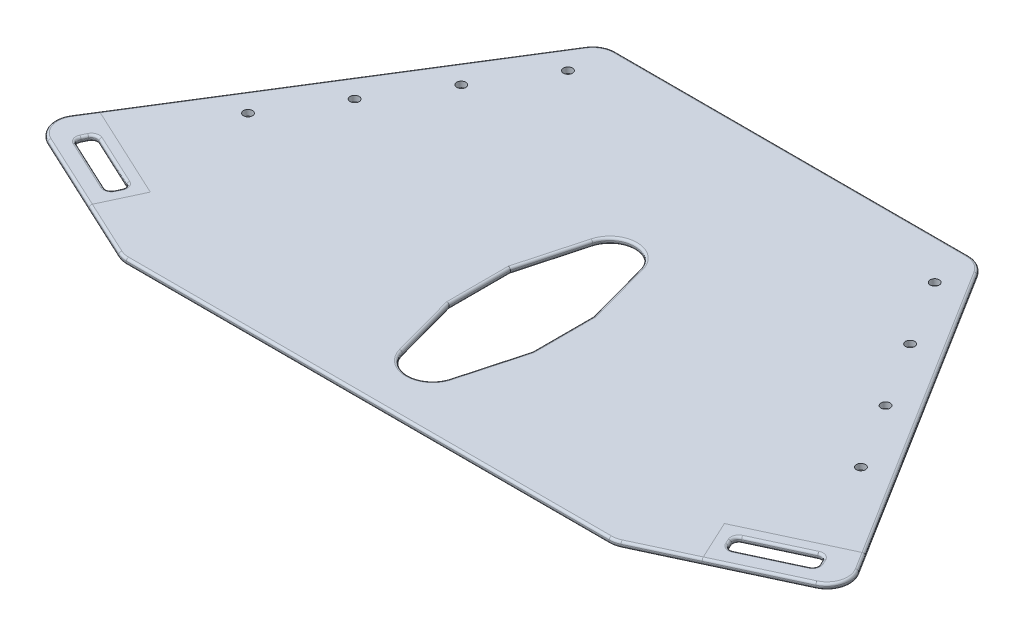
SolidWorks part; units mm, degrees
material "6061 Alloy"
ref_plane "Front Plane" through (0, 0, 0) normal (0, 0, 1) x (1, 0, 0)
ref_plane "Top Plane" through (0, 0, 0) normal (0, 1, 0) x (1, 0, 0)
ref_plane "Right Plane" through (0, 0, 0) normal (1, 0, 0) x (0, 0, -1)
sketch "Sketch1" plane through (0, 0, 0) normal (0, 1, 0) x (1, 0, 0)
  line L0 (0, -251.3064) -> (0, 218.5936) construction
  line L1 (451.3883, -168.1459) -> (273.05, -251.3064)
  line L2 (-451.3883, -168.1459) -> (-209.55, 218.5936)
  line L3 (-209.55, 218.5936) -> (0, 218.5936)
  line L4 (209.55, 218.5936) -> (0, 218.5936)
  line L5 (451.3883, -168.1459) -> (209.55, 218.5936)
  line L6 (-202.1219, 199.0782) -> (-377.1932, -80.8898) construction
  line L7 (-273.05, -251.3064) -> (-451.3883, -168.1459)
  line L8 (273.05, -251.3064) -> (-273.05, -251.3064)
  line L9 (0, -55) -> (0, 55) construction
  line L23 (46.0374, -47.3802) -> (26.459, 24.1588)
  line L24 (46.0374, -115.1266) -> (46.0374, -47.3802)
  line L25 (26.459, -186.6656) -> (46.0374, -115.1266)
  line L26 (-46.0374, -115.1266) -> (-26.459, -186.6656)
  line L27 (-46.0374, -47.3802) -> (-46.0374, -115.1266)
  line L28 (-26.459, 24.1588) -> (-46.0374, -47.3802)
  line L29 (46.0374, -47.3802) -> (26.459, 24.1588)
  line L30 (46.0374, -115.1266) -> (46.0374, -47.3802)
  line L31 (26.459, -186.6656) -> (46.0374, -115.1266)
  line L32 (-46.0374, -115.1266) -> (-26.459, -186.6656)
  line L33 (-46.0374, -47.3802) -> (-46.0374, -115.1266)
  line L34 (-26.459, 24.1588) -> (-46.0374, -47.3802)
  arc A4 (26.459, 24.1588) -> (-26.459, 24.1588) centre (0, 16.9176) ccw
  arc A5 (-26.459, -186.6656) -> (26.459, -186.6656) centre (0, -179.4244) ccw
  arc A6 (26.459, 24.1588) -> (-26.459, 24.1588) centre (0, 16.9176) ccw
  arc A7 (-26.459, -186.6656) -> (26.459, -186.6656) centre (0, -179.4244) ccw
  dimension "D2" = 419.1
  dimension "D3" = 469.9
  dimension "D4" = 44.45
  dimension "D5" = 546.1
  dimension "D6" = 65
  dimension "D1" = 6.35
extrude "Boss-Extrude1" add sketch "Sketch1" along normal blind 6.35
sketch "Sketch2" plane through (0, 6.35, 0) normal (0, 1, 0) x (1, 0, 0)
  line L0 (-342.9, -197.7155) -> (-411.9607, -165.512)
  line L1 (-342.9, -197.7155) -> (-334.8491, -180.4503)
  line L2 (-411.9607, -165.512) -> (-403.9098, -148.2468)
  line L3 (-334.8491, -180.4503) -> (-403.9098, -148.2468)
  line L4 (-342.9, -197.7155) -> (-403.9098, -148.2468) construction
  line L5 (-411.9607, -165.512) -> (-334.8491, -180.4503) construction
  line L6 (-451.3883, -168.1459) -> (-273.05, -251.3064) construction
  point P1 (-373.4049, -172.9811)
  dimension "D1" = 19.05
  dimension "D2" = 76.2
  dimension "D3" = 19.05
  dimension "D4" = 69.85
extrude "Cut-Extrude1" cut sketch "Sketch2" against normal through all
sketch "Sketch7" plane through (0, 6.35, 0) normal (0, 1, 0) x (1, 0, 0)
  line L2 (-329.4819, -168.9402) -> (-398.5425, -136.7367)
  line L3 (-317.9718, -174.3074) -> (-424.2508, -124.7487)
  line L4 (-451.3883, -168.1459) -> (-273.05, -251.3064) construction
  line L5 (-331.3899, -203.0827) -> (-323.339, -185.8176)
  line L6 (-339.4408, -220.3479) -> (-317.9718, -174.3074)
  line L7 (-451.3883, -168.1459) -> (-339.4408, -220.3479)
  line L8 (-209.55, 218.5936) -> (-451.3883, -168.1459) construction
  line L9 (-424.2508, -124.7487) -> (-451.3883, -168.1459)
  line L10 (0, 0) -> (0, -351.854) construction
  line L11 (424.2508, -124.7487) -> (451.3883, -168.1459)
  line L12 (317.9718, -174.3074) -> (424.2508, -124.7487)
  line L13 (339.4408, -220.3479) -> (317.9718, -174.3074)
  line L14 (451.3883, -168.1459) -> (339.4408, -220.3479)
  dimension "D1" = 12.7
  dimension "D2" = 12.7
split line "Split Line1"
fillet "Fillet3" radius 6.35 4 edges at (-334.8491, 3.175, 180.4503) (-342.9, 3.175, 197.7155) (-411.9607, 3.175, 165.512) (-403.9098, 3.175, 148.2468)
fillet "Fillet4" radius 2.54 16 edges at (-337.3208, 0, 181.3499) (-337.3208, 6.35, 181.3499) (-338.8746, 6.35, 189.0829) (-338.8746, 0, 189.0829) (-343.7996, 0, 195.2438) (-343.7996, 6.35, 195.2438) (-377.4303, 6.35, 181.6137) (-377.4303, 0, 181.6137) (-409.489, 0, 164.6124) (-409.489, 6.35, 164.6124) (-407.9352, 6.35, 156.8794) (-407.9352, 0, 156.8794) (-403.0102, 0, 150.7184) (-403.0102, 6.35, 150.7184) (-369.3794, 0, 164.3485) (-369.3794, 6.35, 164.3485)
mirror "Mirror1" about plane through (0, 0, 0) normal (1, 0, 0) of "Fillet3", "Fillet4", "Cut-Extrude1"
hole_wizard "3/8 Clearance Hole1" positions "Sketch4" profile "Sketch3" hole size "3/8" standard "ANSI Inch" end condition up to next
sketch "Sketch4" plane through (0, 6.35, 0) normal (0, 1, 0) x (1, 0, 0)
  point P0 (339.4912, -44.5513)
  point P3 (294.04, 28.1327)
  point P6 (248.5888, 100.8167)
  point P9 (203.1376, 173.5007)
  point P12 (-203.1376, 173.5007)
  point P15 (-248.5888, 100.8167)
  point P18 (-294.04, 28.1327)
  point P21 (-339.4912, -44.5513)
sketch "Sketch3" plane through (339.4912, 6.35, 44.5513) normal (1, 0, 0) x (0, 0, 1)
  line L0 (0, 0) -> (0, 6.35)
  line L1 (0, 6.35) -> (5.0419, 6.35)
  line L2 (5.0419, 6.35) -> (5.0419, 0)
  line L5 (5.0419, 0) -> (0, 0)
  line L11 (0, -6.35) -> (0, 107.95) construction
  dimension "Thru Hole Dia." = 10.0838
  dimension "Thru Hole Depth" = 6.35
fillet "Fillet1" radius 25.4 6 edges at (-209.55, 3.175, -218.5936) (209.55, 3.175, -218.5936) (-451.3883, 3.175, 168.1459) (-273.05, 3.175, 251.3064) (451.3883, 3.175, 168.1459) (273.05, 3.175, 251.3064)
fillet "Fillet2" radius 2.54 16 edges at (36.2482, 0, 11.6107) (0, 0, -44.3496) (36.2482, 0, 150.8961) (0, 0, 206.8564) (36.2482, 6.35, 150.8961) (0, 6.35, 206.8564) (36.2482, 6.35, 11.6107) (0, 6.35, -44.3496) (46.0374, 0, 81.2534) (46.0374, 6.35, 81.2534) (-36.2482, 0, 11.6107) (-46.0374, 0, 81.2534) (-36.2482, 0, 150.8961) (-36.2482, 6.35, 150.8961) (-46.0374, 6.35, 81.2534) (-36.2482, 6.35, 11.6107)
fillet "Fillet5" radius 2.54 28 edges at (-326.5868, 0, -31.4324) (-320.6314, 6.35, -40.956) (0, 0, -218.5936) (326.5868, 0, -31.4324) (351.7567, 0, 214.6049) (0, 0, 251.3064) (-351.7567, 0, 214.6049) (272.9165, 0, 250.7043) (438.9807, 0, 164.4729) (-272.9165, 0, 250.7043) (-438.9807, 0, 164.4729) (207.7865, 0, -215.411) (-207.7865, 0, -215.411) (0, 6.35, -218.5936) (0, 6.35, 251.3064) (308.7971, 6.35, 234.6373) (272.9165, 6.35, 250.7043) (-272.9165, 6.35, 250.7043) (207.7865, 6.35, -215.411) (-207.7865, 6.35, -215.411) (430.2062, 6.35, 134.2723) (-382.4004, 6.35, 200.3155) (-438.9807, 6.35, 164.4729) (438.9807, 6.35, 164.4729) (-430.2062, 6.35, 134.2723) (-308.7971, 6.35, 234.6373) (382.4004, 6.35, 200.3155) (320.6314, 6.35, -40.956)
